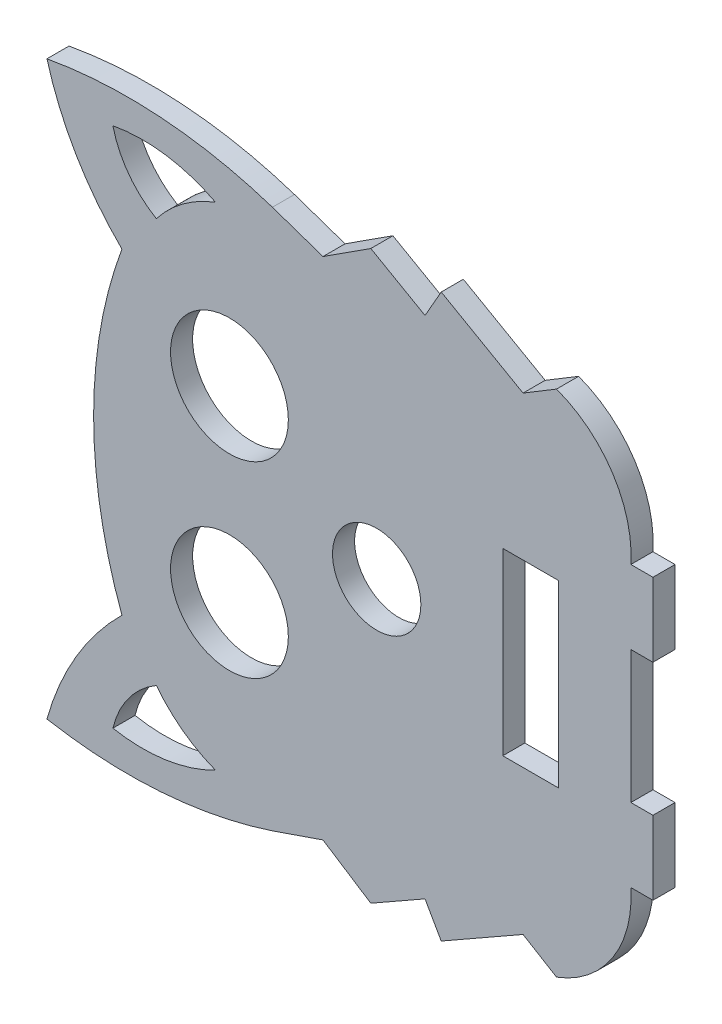
SolidWorks part; units mm, degrees
ref_plane "Front Plane" through (0, 0, 0) normal (0, 0, 1) x (1, 0, 0)
ref_plane "Top Plane" through (0, 0, 0) normal (0, 1, 0) x (1, 0, 0)
ref_plane "Right Plane" through (0, 0, 0) normal (1, 0, 0) x (0, 0, -1)
sketch "Sketch2" plane through (0, 0, 0) normal (0, 0, 1) x (1, 0, 0)
  line L0 (81.0321, 50.1813) -> (81.0321, 60.1813)
  line L1 (81.0321, 60.1813) -> (78.0321, 60.1813)
  line L16 (78.0321, 22.1813) -> (81.0321, 22.1813)
  line L17 (81.0321, 22.1813) -> (81.0321, 32.1813)
  line L18 (81.0321, 32.1813) -> (78.0321, 32.1813)
  line L19 (78.0321, 32.1813) -> (78.0321, 50.1813)
  line L20 (78.0321, 50.1813) -> (81.0321, 50.1813)
  line L49 (78.0321, 41.1813) -> (23.507, 41.1813) construction
  line L50 (29.3426, 77.8618) -> (36.2125, 75.4953)
  line L51 (36.2125, 75.4953) -> (42.71, 79.6915)
  line L52 (42.71, 79.6915) -> (50.0742, 75.4953)
  line L53 (50.0742, 75.4953) -> (52.2746, 79.3569)
  line L54 (52.2746, 79.3569) -> (63.3891, 73.0238)
  line L55 (63.3891, 73.0238) -> (67.9362, 75.7701)
  line L56 (63.3891, 9.3388) -> (67.9362, 6.5926)
  line L57 (52.2746, 3.0057) -> (63.3891, 9.3388)
  line L58 (50.0742, 6.8674) -> (52.2746, 3.0057)
  line L59 (42.71, 2.6711) -> (50.0742, 6.8674)
  line L60 (36.2125, 6.8674) -> (42.71, 2.6711)
  line L61 (29.3426, 4.5008) -> (36.2125, 6.8674)
  line L62 (60.632, 41.1813) -> (68.232, 41.1813) construction
  line L63 (60.632, 53.3813) -> (68.232, 53.3813)
  line L64 (60.632, 53.3813) -> (60.632, 28.9813)
  line L65 (60.632, 28.9813) -> (68.232, 28.9813)
  line L66 (68.232, 53.3813) -> (68.232, 28.9813)
  circle A0 centre (23.507, 53.9313) radius 8
  circle A1 centre (43.507, 41.1813) radius 6
  circle A2 centre (23.507, 28.4313) radius 8
  arc A34 (29.3426, 77.8618) -> (-1.2792, 80.0172) centre (9.7799, 18.5334) ccw
  arc A35 (-1.2792, 80.0172) -> (8.9024, 62.7188) centre (36.2125, 90.4388) ccw
  arc A36 (8.9024, 62.7188) -> (8.9024, 19.6438) centre (67.2985, 41.1813) ccw
  arc A37 (29.3426, 4.5008) -> (-1.2792, 2.3455) centre (9.7799, 63.8292) cw
  arc A38 (-1.2792, 2.3455) -> (8.9024, 19.6438) centre (36.2125, -8.0762) cw
  arc A39 (21.6117, 74.5865) -> (7.6783, 76.612) centre (11.7046, 55.3732) ccw
  arc A40 (7.6783, 76.612) -> (13.5809, 68.637) centre (19.9373, 79.5135) ccw
  arc A41 (13.5809, 68.637) -> (21.6117, 74.5865) centre (28.1138, 57.4149) cw
  arc A42 (7.6783, 5.7506) -> (13.5809, 13.7256) centre (19.9373, 2.8491) cw
  arc A43 (13.5809, 13.7256) -> (21.6117, 7.7761) centre (28.1138, 24.9477) ccw
  arc A44 (21.6117, 7.7761) -> (7.6783, 5.7506) centre (11.7046, 26.9895) cw
  arc A45 (67.9362, 75.7701) -> (78.0321, 60.1813) centre (62.5267, 61.203) cw
  arc A46 (67.9362, 6.5926) -> (78.0321, 22.1813) centre (62.5267, 21.1596) ccw
  dimension "D2" = 12.75
  dimension "D3" = 12.75
  dimension "D5" = 17.125
  dimension "D1" = 7.6
  dimension "D4" = 24.4
extrude "Boss-Extrude1" add sketch "Sketch2" along normal blind 3
